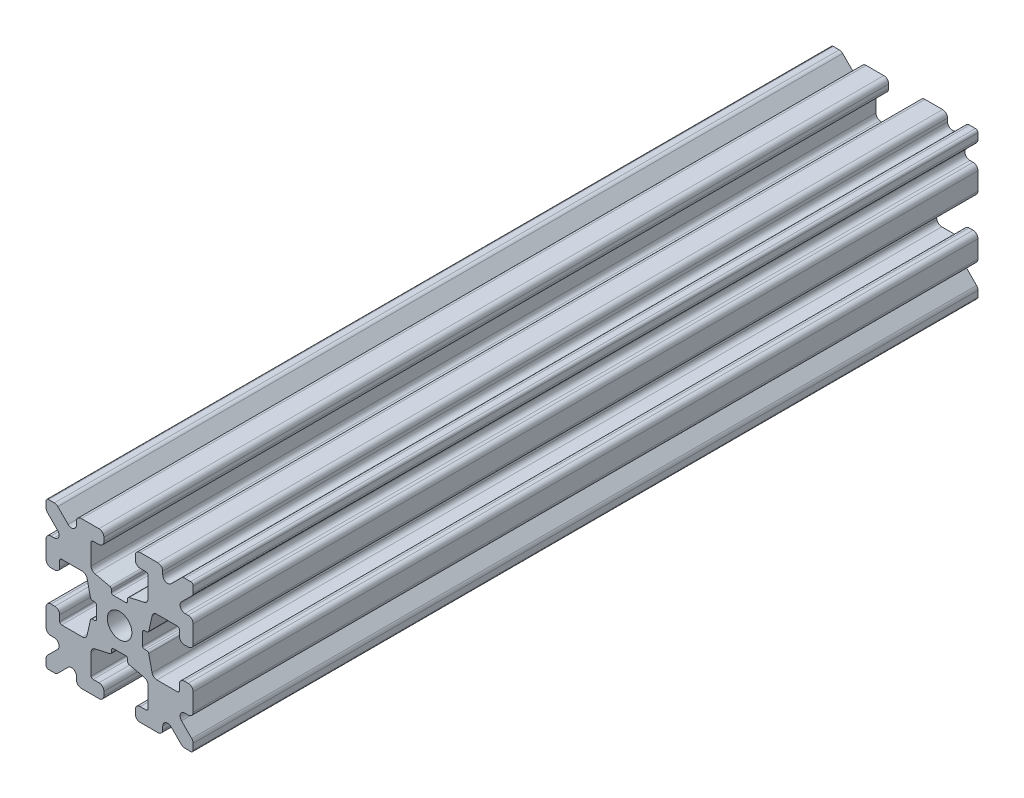
SolidWorks part; units mm, degrees
ref_plane "Front Plane" through (0, 0, 0) normal (0, 0, 1) x (1, 0, 0)
ref_plane "Top Plane" through (0, 0, 0) normal (0, 1, 0) x (1, 0, 0)
ref_plane "Right Plane" through (0, 0, 0) normal (1, 0, 0) x (0, 0, -1)
sketch "Sketch1" plane through (0, 0, 0) normal (0, 0, 1) x (1, 0, 0)
  line L1 (-7.5, -7.5) -> (7.5, -7.5)
  line L2 (-7.5, -7.5) -> (-7.5, 7.5)
  line L3 (-7.5, 7.5) -> (7.5, 7.5)
  line L4 (7.5, -7.5) -> (7.5, 7.5)
  line L5 (-7.5, -7.5) -> (7.5, 7.5) construction
  line L6 (-7.5, 7.5) -> (7.5, -7.5) construction
  circle A0 centre (0, 0) radius 1.25
  point P0 (0, 0)
  dimension "D2" = 2.5
  dimension "D1" = 15
extrude "Boss-Extrude1" add sketch "Sketch1" along normal mid plane 80
fillet "Fillet1" radius 0.25 4 edges at (7.5, -7.5, 0) (-7.5, -7.5, 0) (7.5, 7.5, 0) (-7.5, 7.5, 0)
sketch "Sketch2" plane through (0, 0, 40) normal (0, 0, 1) x (1, 0, 0)
  line L0 (-7.5, 7.25) -> (-7.5, -7.25) construction
  line L1 (-7.5, 1.6) -> (-6.1, 1.6)
  line L2 (-7.5, 1.6) -> (-7.5, -1.6)
  line L3 (-7.5, -1.6) -> (-6.1, -1.6)
  line L4 (-6.1, 1.6) -> (-6.1, 2.9)
  line L5 (0, 0) -> (-12.1036, 0) construction
  line L6 (-6.1, -2.9) -> (-3.4, -2.9)
  line L7 (0, 0) -> (-7.25, 7.25) construction
  line L8 (-6.1, 2.9) -> (-3.4, 2.9)
  line L9 (-3.4, -2.9) -> (-3.4, 2.9)
  line L10 (55, 0) -> (-55, 0) construction
  line L11 (-6.1, -2.9) -> (-6.1, -1.6)
  line L12 (2.9, 6.1) -> (1.6, 6.1)
  line L13 (2.9, 3.4) -> (-2.9, 3.4)
  line L14 (-2.9, 6.1) -> (-2.9, 3.4)
  line L15 (2.9, 6.1) -> (2.9, 3.4)
  line L16 (-1.6, 6.1) -> (-2.9, 6.1)
  line L17 (1.6, 7.5) -> (1.6, 6.1)
  line L18 (-1.6, 7.5) -> (1.6, 7.5)
  line L19 (-1.6, 7.5) -> (-1.6, 6.1)
  line L20 (-1.6, -7.5) -> (-1.6, -6.1)
  line L21 (-1.6, -7.5) -> (1.6, -7.5)
  line L22 (1.6, -7.5) -> (1.6, -6.1)
  line L23 (-1.6, -6.1) -> (-2.9, -6.1)
  line L24 (2.9, -6.1) -> (2.9, -3.4)
  line L25 (-2.9, -6.1) -> (-2.9, -3.4)
  line L26 (2.9, -3.4) -> (-2.9, -3.4)
  line L27 (2.9, -6.1) -> (1.6, -6.1)
  line L28 (6.1, -2.9) -> (6.1, -1.6)
  line L29 (3.4, -2.9) -> (3.4, 2.9)
  line L30 (6.1, 2.9) -> (3.4, 2.9)
  line L31 (6.1, -2.9) -> (3.4, -2.9)
  line L32 (6.1, 1.6) -> (6.1, 2.9)
  line L33 (7.5, -1.6) -> (6.1, -1.6)
  line L34 (7.5, 1.6) -> (7.5, -1.6)
  line L35 (7.5, 1.6) -> (6.1, 1.6)
  dimension "D1" = 3.2
  dimension "D2" = 5.8
  dimension "D3" = 1.4
  dimension "D4" = 2.7
extrude "Cut-Extrude1" cut sketch "Sketch2" against normal through all
sketch "Sketch4" plane through (0, 0, 40) normal (0, 0, 1) x (1, 0, 0)
  line L0 (-3.4, 2.9) -> (-2.75, 0)
  line L1 (55, 0) -> (-55, 0) construction
  line L2 (-2.75, 0) -> (-3.4, -2.9)
  line L3 (-3.4, -2.9) -> (-3.4, 2.9) construction
  line L4 (-3.4, 2.9) -> (-3.4, -2.9)
  line L5 (-2.9, 3.4) -> (0, 2.75)
  line L6 (0, 2.75) -> (2.9, 3.4)
  line L7 (2.9, 3.4) -> (-2.9, 3.4)
  line L8 (3.4, 2.9) -> (2.75, 0)
  line L9 (2.75, 0) -> (3.4, -2.9)
  line L10 (3.4, -2.9) -> (3.4, 2.9)
  line L11 (-2.9, -3.4) -> (0, -2.75)
  line L12 (0, -2.75) -> (2.9, -3.4)
  line L13 (2.9, -3.4) -> (-2.9, -3.4)
  circle A2 centre (0, 0) radius 2.75
  circle A3 centre (0, 0) radius 2.75 construction
  dimension "D1" = 1.5
extrude "Cut-Extrude3" cut sketch "Sketch4" against normal through all
fillet "Fillet3" radius 0.5 16 edges at (-6.1, -1.6, 0) (-7.5, -1.6, 0) (-6.1, 1.6, 0) (-7.5, 1.6, 0) (-1.6, -7.5, 0) (-1.6, -6.1, 0) (1.6, -7.5, 0) (1.6, -6.1, 0) (6.1, -1.6, 0) (7.5, -1.6, 0) (7.5, 1.6, 0) (6.1, 1.6, 0) (1.6, 7.5, 0) (1.6, 6.1, 0) (-1.6, 7.5, 0) (-1.6, 6.1, 0)
fillet "Fillet4" radius 0.5 8 edges at (-3.4, 2.9, 0) (-3.4, -2.9, 0) (2.9, -3.4, 0) (-2.9, -3.4, 0) (3.4, -2.9, 0) (3.4, 2.9, 0) (-2.9, 3.4, 0) (2.9, 3.4, 0)
fillet "Fillet5" radius 3 4 edges at (0, -2.75, 0) (2.75, 0, 0) (-2.75, 0, 0) (0, 2.75, 0)
fillet "Fillet6" radius 0.2 8 edges at (-2.9, -6.1, 0) (2.9, -6.1, 0) (6.1, -2.9, 0) (6.1, 2.9, 0) (2.9, 6.1, 0) (-2.9, 6.1, 0) (-6.1, -2.9, 0) (-6.1, 2.9, 0)
sketch "Sketch5" plane through (0, 0, 40) normal (0, 0, 1) x (1, 0, 0)
  line L0 (0, 0) -> (-7.25, 7.25) construction
  line L1 (-7.5, 6.4393) -> (-5.4607, 4.4)
  line L2 (-6.4393, 7.5) -> (-4.4, 5.4607)
  line L3 (-7.5, 4.4) -> (-5.4607, 4.4)
  line L4 (-3.8003, 2.9) -> (-5.9, 2.9) construction
  line L5 (0, 0) -> (-12.1819, 0) construction
  line L6 (-4.4, 7.5) -> (-4.4, 5.4607)
  line L7 (-2.9, 5.9) -> (-2.9, 3.8003) construction
  line L8 (-7.5, 6.4393) -> (-7.5, 4.4)
  line L9 (-7.5, 7.25) -> (-7.5, 2.1) construction
  line L10 (2.1, -7.5) -> (7.25, -7.5) construction
  line L11 (7.5, -7.25) -> (7.5, -2.1) construction
  line L12 (7.25, 7.5) -> (2.1, 7.5) construction
  line L13 (-2.1, 7.5) -> (-7.25, 7.5) construction
  line L14 (-4.4, 7.5) -> (-6.4393, 7.5)
  line L16 (55, 0) -> (-55, 0) construction
  line L17 (0, 0) -> (0, 10.993) construction
  line L18 (0, -54.6431) -> (0, 54.6431) construction
  line L20 (4.4, 7.5) -> (6.4393, 7.5)
  line L22 (7.5, 6.4393) -> (7.5, 4.4)
  line L23 (4.4, 7.5) -> (4.4, 5.4607)
  line L24 (7.5, 4.4) -> (5.4607, 4.4)
  line L25 (6.4393, 7.5) -> (4.4, 5.4607)
  line L26 (7.5, 6.4393) -> (5.4607, 4.4)
  line L27 (7.5, -6.4393) -> (5.4607, -4.4)
  line L28 (6.4393, -7.5) -> (4.4, -5.4607)
  line L29 (7.5, -4.4) -> (5.4607, -4.4)
  line L30 (4.4, -7.5) -> (4.4, -5.4607)
  line L31 (7.5, -6.4393) -> (7.5, -4.4)
  line L33 (4.4, -7.5) -> (6.4393, -7.5)
  line L36 (-4.4, -7.5) -> (-6.4393, -7.5)
  line L38 (-7.5, -6.4393) -> (-7.5, -4.4)
  line L39 (-4.4, -7.5) -> (-4.4, -5.4607)
  line L40 (-7.5, -4.4) -> (-5.4607, -4.4)
  line L41 (-6.4393, -7.5) -> (-4.4, -5.4607)
  line L42 (-7.5, -6.4393) -> (-5.4607, -4.4)
  dimension "D1" = 1.5
  dimension "D2" = 1.5
  dimension "D3" = 1.5
extrude "Cut-Extrude4" cut sketch "Sketch5" against normal through all
fillet "Fillet8" radius 0.5 24 edges at (-5.4607, 4.4, 0) (-7.5, 4.4, 0) (-5.4607, -4.4, 0) (-7.5, -4.4, 0) (-4.4, -7.5, 0) (-4.4, -5.4607, 0) (4.4, -7.5, 0) (4.4, -5.4607, 0) (5.4607, -4.4, 0) (7.5, -4.4, 0) (7.5, 4.4, 0) (5.4607, 4.4, 0) (4.4, 5.4607, 0) (4.4, 7.5, 0) (-4.4, 5.4607, 0) (-4.4, 7.5, 0) (-6.4393, 7.5, 0) (-7.5, 6.4393, 0) (6.4393, 7.5, 0) (7.5, 6.4393, 0) (6.4393, -7.5, 0) (7.5, -6.4393, 0) (-6.4393, -7.5, 0) (-7.5, -6.4393, 0)
sketch "Sketch6" plane through (0, 0, 40) normal (0, 0, 1) x (1, 0, 0)
  line L0 (0, 0) -> (0, 11.013) construction
  line L1 (0.6561, 2.8971) -> (2.1235, 2.8971) construction
  line L2 (0, -54.6431) -> (0, 54.6431) construction
  line L3 (0, 0) -> (7.25, 7.25) construction
  line L4 (7.5, 0.8255) -> (7.5, -0.8255)
  line L5 (2.3471, 0.8255) -> (7.5, 0.8255)
  line L6 (0, 0) -> (12.4016, 0) construction
  line L7 (0.8255, -7.5) -> (-0.8255, -7.5)
  line L8 (2.3471, -0.8255) -> (2.3471, 0.8255)
  line L9 (0.8255, -2.3471) -> (0.8255, -7.5)
  line L10 (7.5, -0.8255) -> (2.3471, -0.8255)
  line L11 (-7.5, -0.8255) -> (-2.3471, -0.8255)
  line L12 (-2.3471, -0.8255) -> (-2.3471, 0.8255)
  line L13 (-0.8255, -2.3471) -> (0.8255, -2.3471)
  line L14 (-0.8255, 7.5) -> (-0.8255, 2.3471)
  line L15 (-0.8255, 2.3471) -> (0.8255, 2.3471)
  line L16 (-0.8255, -7.5) -> (-0.8255, -2.3471)
  line L17 (0.8255, 2.3471) -> (0.8255, 7.5)
  line L18 (0.8255, 7.5) -> (-0.8255, 7.5)
  line L19 (3.9, 7.5) -> (2.1, 7.5) construction
  line L20 (-2.3471, 0.8255) -> (-7.5, 0.8255)
  line L21 (-7.5, 0.8255) -> (-7.5, -0.8255)
  point P5 (0, -2.5973)
  point P7 (0, 2.5973)
  dimension "D3" = 0.55
  dimension "D1" = 1.651
extrude "Cut-Extrude5" cut sketch "Sketch6" against normal through all
fillet "Fillet10" radius 0.2 16 edges at (-2.935, 0.8255, 0) (-2.935, -0.8255, 0) (2.935, -0.8255, 0) (2.935, 0.8255, 0) (0.8255, 2.935, 0) (-0.8255, 2.935, 0) (-2.3471, 0.8255, 0) (-2.3471, -0.8255, 0) (0.8255, 2.3471, 0) (-0.8255, 2.3471, 0) (2.3471, 0.8255, 0) (2.3471, -0.8255, 0) (0.8255, -2.935, 0) (0.8255, -2.3471, 0) (-0.8255, -2.3471, 0) (-0.8255, -2.935, 0)
